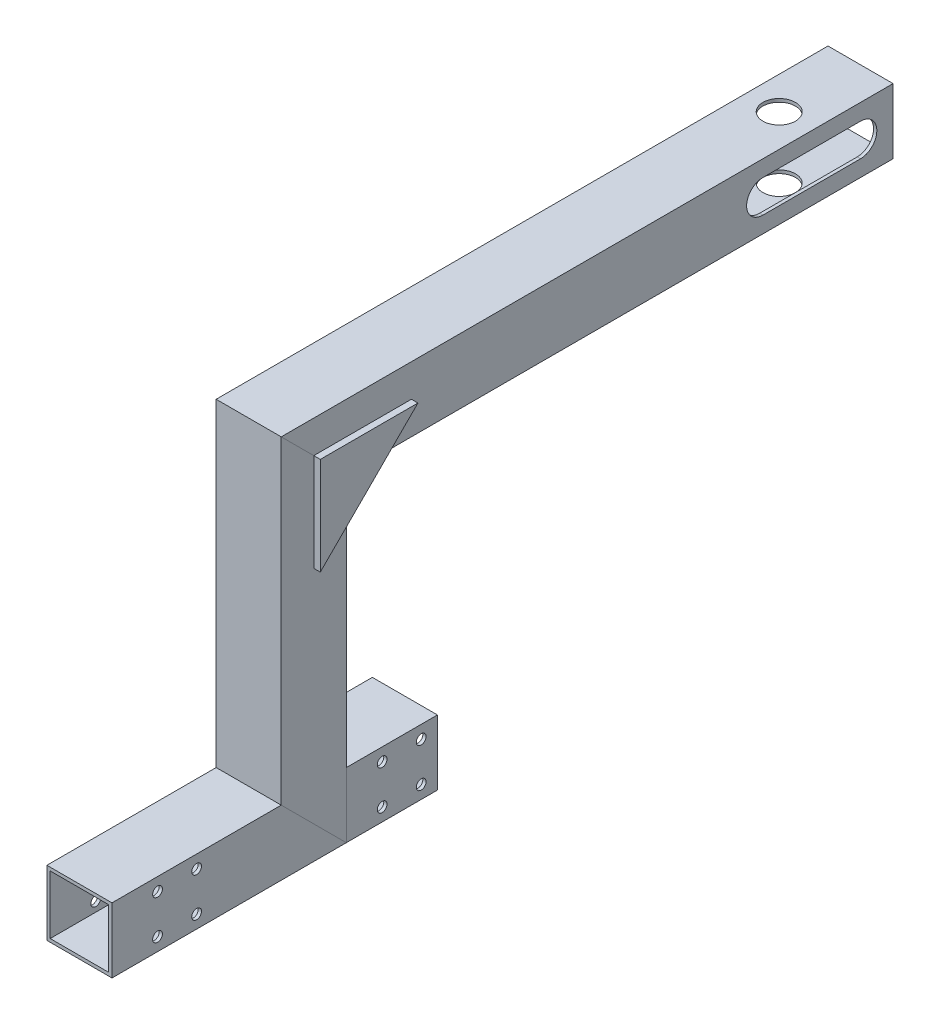
SolidWorks part; units mm, degrees
material "6063-O"
ref_plane "Front" through (0, 0, 0) normal (0, 0, 1) x (1, 0, 0)
ref_plane "Top" through (0, 0, 0) normal (0, 1, 0) x (1, 0, 0)
ref_plane "Right" through (0, 0, 0) normal (1, 0, 0) x (0, 0, -1)
sketch "草图1" plane through (0, 0, 0) normal (1, 0, 0) x (0, 0, -1)
  line L0 (0, 0) -> (62, 0)
  line L1 (62, 0) -> (62, 98)
  line L2 (62, 98) -> (240, 98)
  line L3 (62, 0) -> (125, 0)
  dimension "D1" = 62
  dimension "D2" = 98
  dimension "D3" = 178
  dimension "D4" = 63
other "铝管 20X20X1(1)"
ref_plane "基准面1" through (0, 0, 0) normal (0, 0, -1) x (0, 1, 0)
sketch "草图14" plane through (0, 0, 0) normal (0, 0, -1) x (0, 1, 0)
  line L1 (-10, -10) -> (10, -10)
  line L2 (-10, -10) -> (-10, 10)
  line L3 (-10, 10) -> (10, 10)
  line L4 (10, -10) -> (10, 10)
  line L5 (-10, -10) -> (10, 10) construction
  line L6 (-10, 10) -> (10, -10) construction
  line L7 (-9, -9) -> (9, -9)
  line L8 (-9, -9) -> (-9, 9)
  line L9 (-9, 9) -> (9, 9)
  line L10 (9, -9) -> (9, 9)
  line L11 (-9, -9) -> (9, 9) construction
  line L12 (-9, 9) -> (9, -9) construction
  point P0 (0, 0)
  point P6 (0, 0)
  point P11 (0, 0)
  dimension "D1" = 20
  dimension "D2" = 20
  dimension "D3" = 18
  dimension "D4" = 18
sketch "草图12" plane through (10, 0, 0) normal (1, 0, 0) x (0, 0, -1)
  line L0 (0, 0) -> (34.5882, 0) construction
  line L1 (0, 10) -> (0, -10) construction
  line L2 (6, 5) -> (34, 5) construction
  line L3 (20, 5) -> (20, -26.9272) construction
  circle A0 centre (6, 5) radius 1.5 construction
  circle A1 centre (34, 5) radius 1.5 construction
  circle A2 centre (34, -5) radius 1.5 construction
  circle A3 centre (6, -5) radius 1.5 construction
  circle A4 centre (14, 6) radius 1.5
  circle A5 centre (14, -6) radius 1.5
  circle A6 centre (26, -6) radius 1.5
  circle A7 centre (26, 6) radius 1.5
  dimension "D1" = 3
  dimension "D2" = 3
  dimension "D6" = 3
  dimension "D7" = 3
  dimension "D8" = 3
  dimension "D9" = 3
  dimension "D3" = 5
  dimension "D4" = 28
  dimension "D5" = 6
  dimension "D10" = 12
  dimension "D11" = 12
extrude "切除-拉伸1" cut sketch "草图12" against normal through all
sketch "草图15" plane through (10, 0, 0) normal (1, 0, 0) x (0, 0, -1)
  line L0 (20, 10) -> (20, -10) construction
  line L1 (52, 10) -> (0, 10) construction
  line L2 (72, -10) -> (0, -10) construction
  line L3 (0, 10) -> (0, -10) construction
  line L4 (215, 149.4201) -> (215, 66.8372) construction
  line L5 (206.1971, 98) -> (287.2027, 98) construction
  line L6 (240, 108) -> (52, 108) construction
  line L7 (200, 98) -> (230, 98) construction
  line L8 (200, 103) -> (230, 103)
  line L9 (200, 93) -> (230, 93)
  arc A0 (200, 103) -> (200, 93) centre (200, 98) ccw
  arc A1 (230, 93) -> (230, 103) centre (230, 98) ccw
  point P16 (215, 98)
  dimension "D1" = 20
  dimension "D2" = 195
  dimension "D3" = 10
  dimension "D4" = 10
  dimension "D5" = 30
extrude "切除-拉伸3" cut sketch "草图15" against normal through all
sketch "草图16" plane through (0, 88, 0) normal (0, -1, 0) x (1, 0, 0)
  line L0 (10, -230) -> (10, -200) construction
  line L1 (10, -230) -> (10, -200)
  line L2 (10, -215) -> (-10, -215) construction
  line L3 (-10, -240) -> (-10, -72) construction
  circle A0 centre (0, -215) radius 5
  dimension "D1" = 10
extrude "切除-拉伸4" cut sketch "草图16" against normal through all contours L2 A0 | A0 L2
sketch "草图17" plane through (10, 0, 0) normal (1, 0, 0) x (0, 0, -1)
  line L0 (0, 0) -> (62, 0) construction
  line L1 (52, 10) -> (72, -10) construction
  line L2 (0, 10) -> (0, -10) construction
  circle A0 centre (68, 6) radius 1.5 construction
  circle A1 centre (80, 6) radius 1.5 construction
  circle A2 centre (68, -6) radius 1.5 construction
  circle A3 centre (80, -6) radius 1.5 construction
  circle A4 centre (83, 6) radius 1.5
  circle A5 centre (95, 6) radius 1.5
  circle A6 centre (83, -6) radius 1.5
  circle A7 centre (95, -6) radius 1.5
  dimension "D1" = 3
  dimension "D2" = 3
  dimension "D3" = 3
  dimension "D4" = 3
  dimension "D5" = 12
  dimension "D6" = 12
  dimension "D7" = 68
  dimension "D9" = 15
  dimension "D8" = 2
ref_plane "基准面2" through (0, 98, 0) normal (0, -1, 0) x (-1, 0, 0)
sketch "草图18" [suppressed] plane through (0, 120, 0) normal (0, -1, 0) x (-1, 0, 0)
  line L0 (0, 260) -> (42.4225, 260) construction
  line L1 (10, 260) -> (40, 260)
  line L2 (10, 285) -> (10, 115) construction
  dimension "D1" = 30
other "铝管 20X20X1(12)" [suppressed]
ref_plane "基准面3" through (-10, 120, -260) normal (-1, 0, 0) x (0, 0, -1)
sketch "草图19" plane through (-10, 120, -260) normal (-1, 0, 0) x (0, 0, -1)
  line L1 (-10, -10) -> (10, -10)
  line L2 (-10, -10) -> (-10, 10)
  line L3 (-10, 10) -> (10, 10)
  line L4 (10, -10) -> (10, 10)
  line L5 (-10, -10) -> (10, 10) construction
  line L6 (-10, 10) -> (10, -10) construction
  line L7 (-9, -9) -> (9, -9)
  line L8 (-9, -9) -> (-9, 9)
  line L9 (-9, 9) -> (9, 9)
  line L10 (9, -9) -> (9, 9)
  line L11 (-9, -9) -> (9, 9) construction
  line L12 (-9, 9) -> (9, -9) construction
  point P0 (0, 0)
  point P6 (0, 0)
  point P11 (0, 0)
  dimension "D1" = 20
  dimension "D2" = 20
  dimension "D3" = 18
  dimension "D4" = 18
sketch "草图20" [suppressed] plane through (0, 110, 0) normal (0, -1, 0) x (1, 0, 0)
  line L0 (-10, -260) -> (-40, -260) construction
  line L1 (-40, -270) -> (-40, -250) construction
  circle A0 centre (-30, -260) radius 3
  dimension "D1" = 6
  dimension "D2" = 10
extrude "切除-拉伸6" [suppressed] cut sketch "草图20" against normal through all
sketch "草图21" plane through (10, 0, 0) normal (1, 0, 0) x (0, 0, -1)
  line L0 (62, 98) -> (62, 68)
  line L1 (72, 88) -> (52, 108) construction
  line L2 (62, 68) -> (92, 98)
  line L3 (92, 98) -> (62, 98)
  dimension "D1" = 30
  dimension "D2" = 135
extrude "凸台-拉伸1" add sketch "草图21" along normal blind 2 separate body
sketch "草图22" plane through (-10, 0, 0) normal (-1, 0, 0) x (0, 0, 1)
  line L3 (-62, 98) -> (-92, 98)
  line L4 (-62, 68) -> (-62, 98)
  line L5 (-92, 98) -> (-62, 68)
  line L6 (-62, 98) -> (-92, 98)
  line L7 (-62, 68) -> (-62, 98)
  line L8 (-92, 98) -> (-62, 68)
  dimension "D1" = 0
extrude "凸台-拉伸2" add sketch "草图22" along normal blind 2 separate body
extrude "切除-拉伸7" cut sketch "草图17" against normal through all
sketch "草图23" plane through (10, 0, 0) normal (1, 0, 0) x (0, 0, -1)
  line L0 (125, 10) -> (72, 10) construction
  line L1 (125, -10) -> (100, -10)
  line L2 (125, -10) -> (125, 10)
  line L3 (125, 10) -> (100, 10)
  line L4 (100, -10) -> (100, 10)
  line L5 (72, 88) -> (72, -10) construction
  dimension "D1" = 28
extrude "切除-拉伸8" cut sketch "草图23" against normal through all
